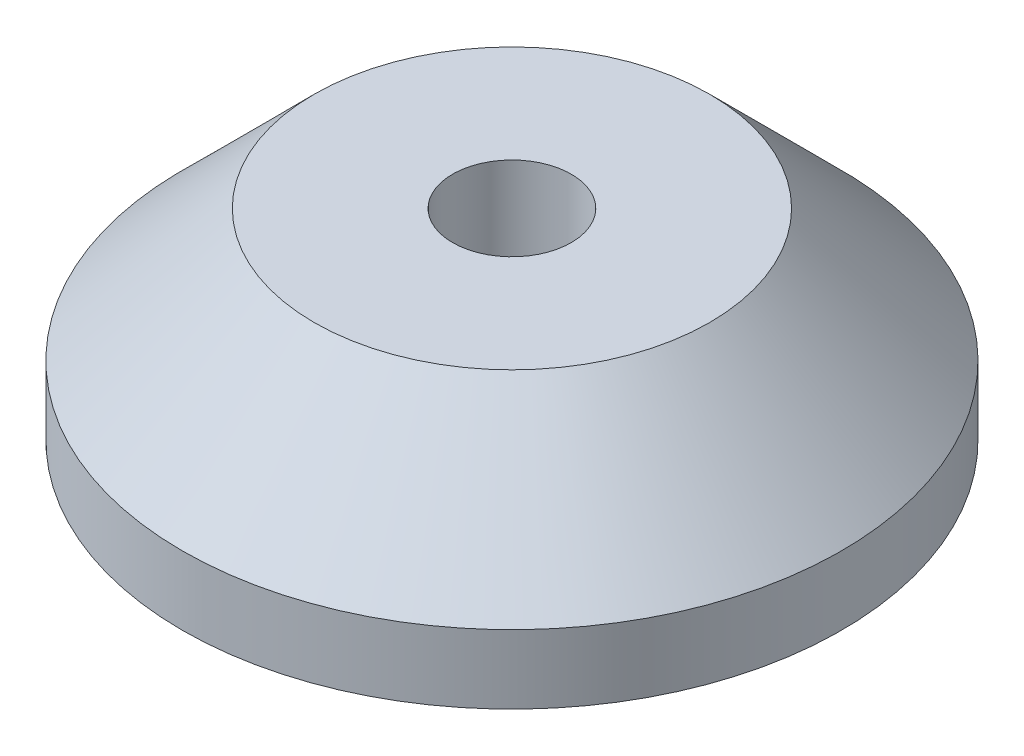
SolidWorks part; units mm, degrees
ref_plane "Front Plane" through (0, 0, 0) normal (0, 0, 1) x (1, 0, 0)
ref_plane "Top Plane" through (0, 0, 0) normal (0, 1, 0) x (1, 0, 0)
ref_plane "Right Plane" through (0, 0, 0) normal (1, 0, 0) x (0, 0, -1)
sketch "Sketch1" plane through (0, 0, 0) normal (0, 1, 0) x (1, 0, 0)
  circle A0 centre (0, 0) radius 31.75
  circle A1 centre (0, 0) radius 12.827
  dimension "D1" = 63.5
  dimension "D2" = 25.654
extrude "Boss-Extrude1" add sketch "Sketch1" along normal blind 5.1054
sketch "Sketch2" plane through (0, 5.1054, 0) normal (0, 1, 0) x (1, 0, 0)
  circle A0 centre (0, 0) radius 31.75
  circle A1 centre (0, 0) radius 5.715
  circle A2 centre (0, 0) radius 31.75 construction
  dimension "D1" = 11.43
extrude "Boss-Extrude2" add sketch "Sketch2" along normal blind 14.224
chamfer "Chamfer1" distance 5.08 angle 45 1 edges at (0, 0, 12.827)
chamfer "Chamfer2" distance 12.7 angle 45 1 edges at (0, 19.3294, 31.75)
